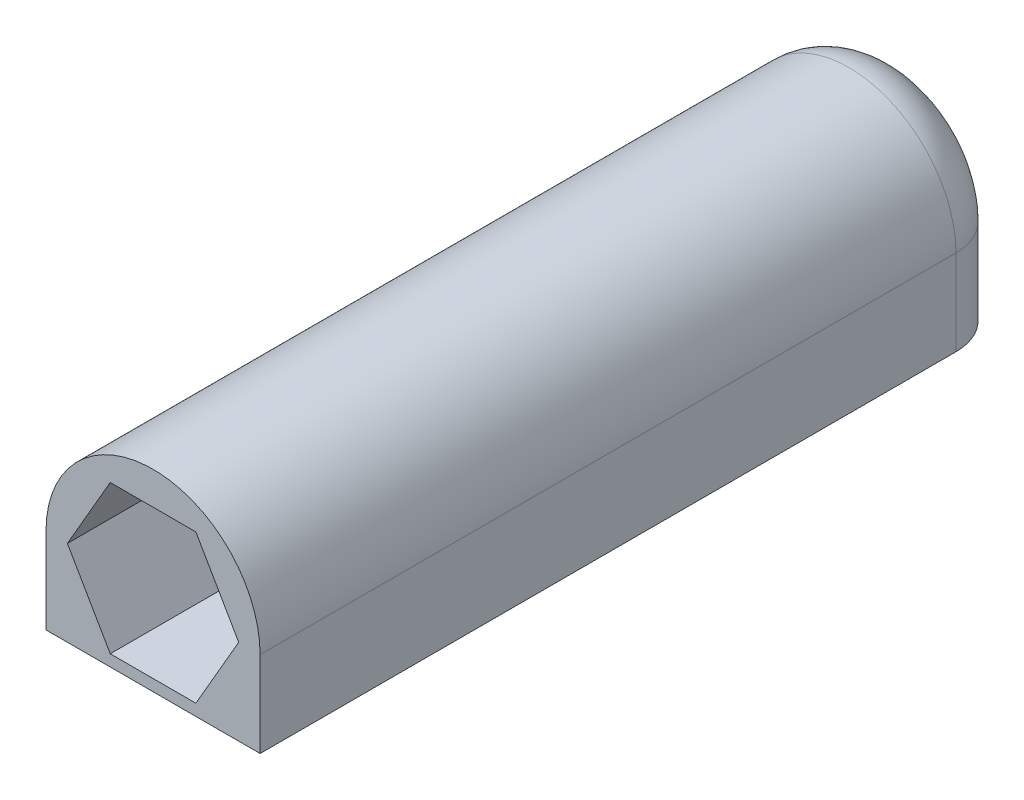
SolidWorks part; units mm, degrees
material "ABS"
ref_plane "Front Plane" through (0, 0, 0) normal (0, 0, 1) x (1, 0, 0)
ref_plane "Top Plane" through (0, 0, 0) normal (0, 1, 0) x (1, 0, 0)
ref_plane "Right Plane" through (0, 0, 0) normal (1, 0, 0) x (0, 0, -1)
sketch "Sketch2" plane through (0, 0, 0) normal (0, 0, 1) x (1, 0, 0)
  line L2 (-12.7, 0) -> (-12.7, -10.16)
  line L3 (-12.7, -10.16) -> (12.7, -10.16)
  line L4 (12.7, 0) -> (12.7, -10.16)
  arc A0 (12.7, 0) -> (-12.7, 0) centre (0, 0) ccw
  dimension "D1" = 25.4
  dimension "D2" = 10.16
extrude "Boss-Extrude1" add sketch "Sketch2" against normal blind 88.9
sketch "Sketch3" plane through (0, 0, 0) normal (0, 0, 1) x (1, 0, 0)
  line L1 (10.16, 0) -> (5.08, 8.7988)
  line L2 (5.08, 8.7988) -> (-5.08, 8.7988)
  line L3 (-5.08, 8.7988) -> (-10.16, 0)
  line L4 (-10.16, 0) -> (-5.08, -8.7988)
  line L5 (-5.08, -8.7988) -> (5.08, -8.7988)
  line L6 (5.08, -8.7988) -> (10.16, 0)
  circle A0 centre (0, 0) radius 10.16 construction
extrude "Cut-Extrude1" cut sketch "Sketch3" against normal blind 30.48
ref_plane "Plane1" through (0, 0, -30.48) normal (0, 0, 1) x (1, 0, 0)
sketch "Sketch4" plane through (0, 0, -30.48) normal (0, 0, 1) x (1, 0, 0)
  line L0 (-12.7, -10.16) -> (12.7, -10.16) construction
  line L2 (-10.16, 0) -> (-10.16, -10.16)
  line L4 (10.16, 0) -> (10.16, -10.16)
  line L7 (-10.16, -10.16) -> (-10.16, -11.5668)
  line L8 (-10.16, -11.5668) -> (10.16, -11.5668)
  line L9 (10.16, -10.16) -> (10.16, -11.5668)
  arc A0 (10.16, 0) -> (-10.16, 0) centre (0, 0) ccw
  dimension "D1" = 20.32
extrude "Cut-Extrude2" cut sketch "Sketch4" against normal blind 45.72
sketch "Sketch5" plane through (0, 0, -88.9) normal (0, 0, -1) x (-1, 0, 0)
  line L0 (12.7, -10.16) -> (-12.7, -10.16) construction
  circle A0 centre (0, 2.54) radius 2.794
  dimension "D1" = 5.588
  dimension "D2" = 12.7
extrude "Cut-Extrude3" cut sketch "Sketch5" against normal blind 7.62
sketch "Sketch6" plane through (0, 0, -88.9) normal (0, 0, -1) x (-1, 0, 0)
  circle A0 centre (0, 2.54) radius 3.175
curve "Helix/Spiral1" pitch 0.8467 height 7.62 turns 9
ref_plane "Plane2" through (2.2451, 4.7851, -81.28) normal (-0.7065, 0.7065, 0.0424) x (0.03, -0.03, 0.9991)
sketch "Sketch7" plane through (2.2451, 4.7851, -81.28) normal (-0.7065, 0.7065, 0.0424) x (0.03, -0.03, 0.9991)
  line L0 (-0.4746, 0) -> (0.9044, 0) construction
  line L1 (-7.6131, -21.1355) -> (81.2069, -21.1355) construction
  line L2 (0, 0) -> (0, -1.5133) construction
  line L3 (0.381, 0) -> (0, -0.635)
  line L4 (0, -0.635) -> (-0.381, 0)
  line L5 (-0.381, 0) -> (0.381, 0)
  dimension "D1" = 0.635
  dimension "D2" = 0.762
sweep "Sweep1" add profiles "Sketch7" path "Helix/Spiral1"
sketch "Sketch8" plane through (0, 0, 0) normal (1, 0, 0) x (0, 0, -1)
  line L0 (88.9, 0) -> (88.9, 12.7) construction
  line L1 (88.9, 9.0105) -> (92.0197, 9.0105)
  line L2 (88.9, 9.0105) -> (88.9, -1.9858)
  line L3 (88.9, -1.9858) -> (92.0197, -1.9858)
  line L4 (92.0197, 9.0105) -> (92.0197, -1.9858)
extrude "Cut-Extrude4" cut sketch "Sketch8" against normal mid plane 25.4
fillet "Fillet1" radius 6.35 3 edges at (-12.7, -5.08, -88.9) (12.7, -5.08, -88.9) (0, 12.7, -88.9)
